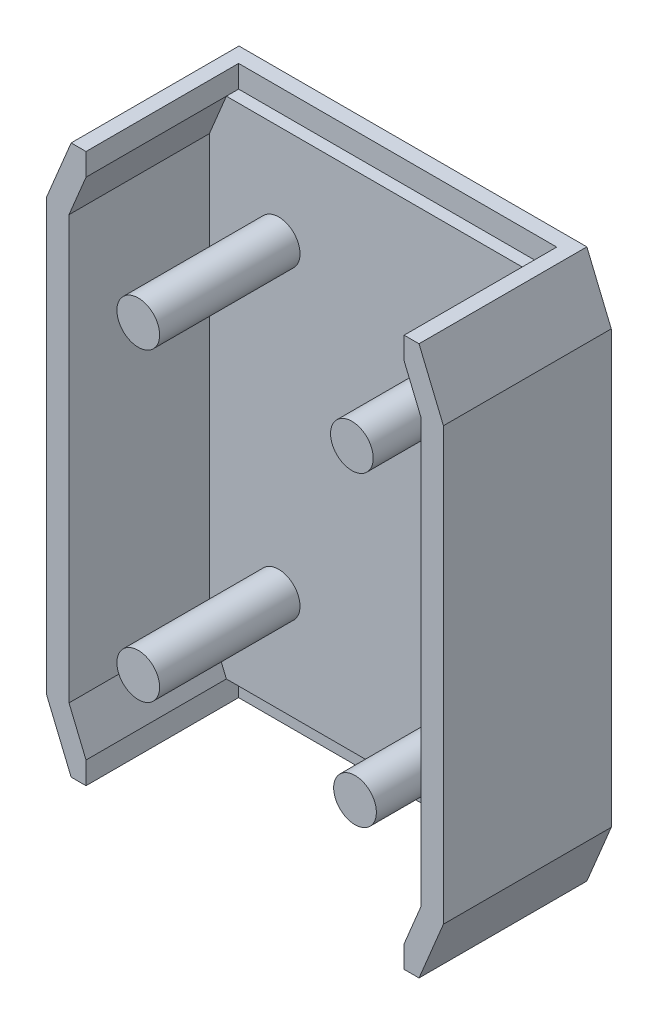
SolidWorks part; units mm, degrees
ref_plane "Front Plane" through (0, 0, 0) normal (0, 0, 1) x (1, 0, 0)
ref_plane "Top Plane" through (0, 0, 0) normal (0, 1, 0) x (1, 0, 0)
ref_plane "Right Plane" through (0, 0, 0) normal (1, 0, 0) x (0, 0, -1)
sketch "Sketch1" plane through (0, 0, 0) normal (0, 0, 1) x (1, 0, 0)
  line L0 (36.195, 57.15) -> (41.275, 44.9144)
  line L1 (-41.275, 57.15) -> (41.275, 57.15)
  line L2 (-41.275, 57.15) -> (-41.275, -57.15)
  line L3 (-41.275, -57.15) -> (41.275, -57.15)
  line L4 (41.275, 57.15) -> (41.275, -57.15)
  line L5 (-41.275, 57.15) -> (41.275, -57.15) construction
  line L6 (-41.275, -57.15) -> (41.275, 57.15) construction
  line L7 (0, 33.4719) -> (0, -22.1917) construction
  line L8 (-26.0475, 0) -> (21.028, 0) construction
  line L9 (-36.195, 57.15) -> (-41.275, 44.9144)
  line L10 (36.195, -57.15) -> (41.275, -44.9144)
  line L11 (-36.195, -57.15) -> (-41.275, -44.9144)
  point P0 (0, 0)
  dimension "D1" = 82.55
  dimension "D2" = 114.3
  dimension "D3" = 5.08
extrude "Boss-Extrude1" add sketch "Sketch1" along normal blind 5.715 contours L11 L3 L10 L4 L0 L1 L9 L2
sketch "Sketch2" plane through (0, 0, 5.715) normal (0, 0, 1) x (1, 0, 0)
  line L0 (-36.2798, 57.277) -> (-41.402, 44.9397)
  line L1 (-41.402, 44.9397) -> (-41.402, -44.9397)
  line L2 (-41.402, -44.9397) -> (-36.2798, -57.277)
  line L3 (-36.2798, -57.277) -> (36.2798, -57.277)
  line L4 (36.2798, -57.277) -> (41.402, -44.9397)
  line L5 (41.402, -44.9397) -> (41.402, 44.9397)
  line L6 (41.402, 44.9397) -> (36.2798, 57.277)
  line L7 (36.2798, 57.277) -> (-36.2798, 57.277)
  line L42 (41.275, 44.9144) -> (36.195, 57.15)
  line L43 (36.195, 57.15) -> (-36.195, 57.15)
  line L44 (-36.195, 57.15) -> (-41.275, 44.9144)
  line L45 (-41.275, 44.9144) -> (-41.275, -44.9144)
  line L46 (-41.275, -44.9144) -> (-36.195, -57.15)
  line L47 (-36.195, -57.15) -> (36.195, -57.15)
  line L48 (36.195, -57.15) -> (41.275, -44.9144)
  line L49 (41.275, -44.9144) -> (41.275, 44.9144)
  line L50 (36.6395, 43.9904) -> (33.1004, 52.5145)
  line L51 (36.6395, -43.9904) -> (36.6395, 43.9904)
  line L52 (33.1004, 52.5145) -> (-33.1004, 52.5145)
  line L53 (33.1004, -52.5145) -> (36.6395, -43.9904)
  line L54 (-33.1004, -52.5145) -> (33.1004, -52.5145)
  line L55 (-36.6395, -43.9904) -> (-33.1004, -52.5145)
  line L56 (-36.6395, 43.9904) -> (-36.6395, -43.9904)
  line L57 (-33.1004, 52.5145) -> (-36.6395, 43.9904)
  line L58 (36.6395, 43.9904) -> (33.1004, 52.5145)
  line L59 (36.6395, -43.9904) -> (36.6395, 43.9904)
  line L60 (33.1004, 52.5145) -> (-33.1004, 52.5145)
  line L61 (33.1004, -52.5145) -> (36.6395, -43.9904)
  line L62 (-33.1004, -52.5145) -> (33.1004, -52.5145)
  line L63 (-36.6395, -43.9904) -> (-33.1004, -52.5145)
  line L64 (-36.6395, 43.9904) -> (-36.6395, -43.9904)
  line L65 (-33.1004, 52.5145) -> (-36.6395, 43.9904)
  line M9 (-41.275, -44.9144) -> (-36.195, -57.15)
  line M10 (-36.195, -57.15) -> (36.195, -57.15)
  line M11 (36.195, -57.15) -> (41.275, -44.9144)
  line M12 (41.275, -44.9144) -> (41.275, 44.9144)
  line M13 (41.275, 44.9144) -> (36.195, 57.15)
  line M14 (36.195, 57.15) -> (-36.195, 57.15)
  line M15 (-36.195, 57.15) -> (-41.275, 44.9144)
  line M16 (-41.275, 44.9144) -> (-41.275, -44.9144)
  dimension "D1" = 4.6355
  dimension "D2" = 4.6355
  dimension "D3" = 4.7625
extrude "Boss-Extrude2" add sketch "Sketch2" along normal blind 29.21 contours L65 L60 L58 L59 L61 L62 L63 L64 M16 M9 M10 M11 M12 M13 M14 M15
sketch "Sketch3" plane through (0, 0, 34.925) normal (0, 0, 1) x (1, 0, 0)
  line L0 (36.195, 57.15) -> (-36.195, 57.15) construction
  line L1 (-33.1004, 52.5145) -> (33.1004, 52.5145)
  line L2 (-33.1004, 52.5145) -> (-33.1004, 57.15)
  line L3 (-33.1004, 57.15) -> (33.1004, 57.15)
  line L4 (33.1004, 52.5145) -> (33.1004, 57.15)
extrude "Cut-Extrude1" cut sketch "Sketch3" against normal blind 31.75
mirror "Mirror1" about plane through (0, 0, 0) normal (0, 1, 0) of "Cut-Extrude1"
sketch "Sketch4" plane through (0, 0, 5.715) normal (0, 0, 1) x (1, 0, 0)
  line L0 (33.1004, 57.15) -> (-33.1004, 57.15) construction
  line L1 (-41.275, 44.9144) -> (-41.275, -44.9144) construction
  line L2 (33.1004, -57.15) -> (-33.1004, -57.15) construction
  circle A0 centre (22.8749, -31.75) radius 4.445
  circle A1 centre (-22.225, -31.75) radius 4.445
  circle A2 centre (22.225, 31.75) radius 4.445
  circle A3 centre (-22.225, 31.75) radius 4.445
  point P10 (0, 0)
  dimension "D1" = 8.89
  dimension "D2" = 8.89
  dimension "D3" = 8.89
  dimension "D4" = 8.89
  dimension "D5" = 25.4
  dimension "D6" = 25.4
  dimension "D7" = 44.45
  dimension "D8" = 19.05
  dimension "D9" = 0
  dimension "D10" = 25.4
  dimension "D11" = 25.4
extrude "Boss-Extrude3" add sketch "Sketch4" along normal blind 29.21
